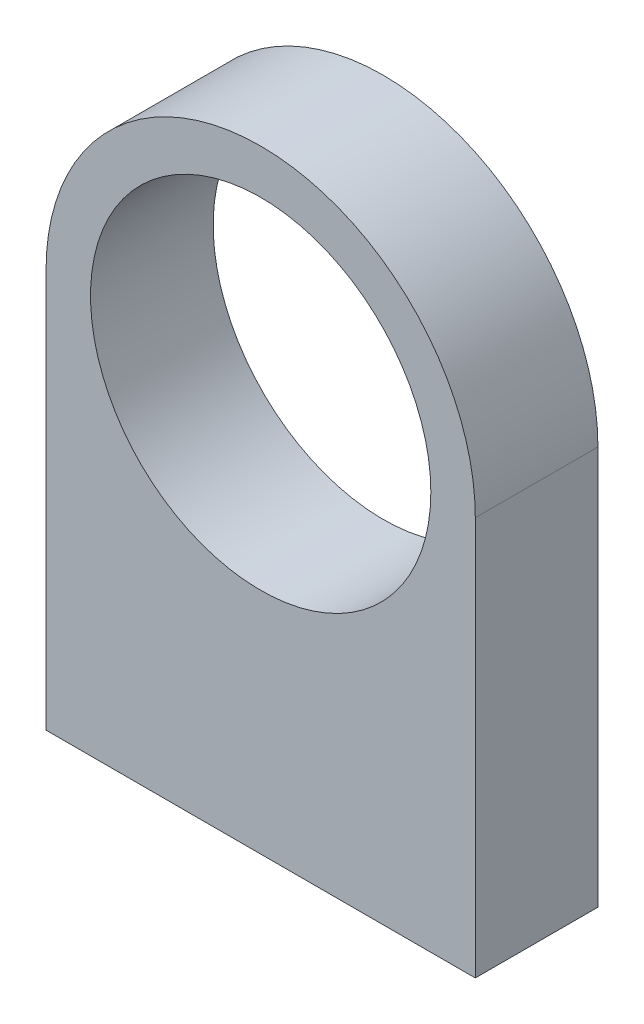
SolidWorks part; units mm, degrees
ref_plane "Plan de face" through (0, 0, 0) normal (0, 0, 1) x (1, 0, 0)
ref_plane "Plan de dessus" through (0, 0, 0) normal (0, 1, 0) x (1, 0, 0)
ref_plane "Plan de droite" through (0, 0, 0) normal (1, 0, 0) x (0, 0, -1)
sketch "Esquisse1" plane through (0, 0, 0) normal (0, 0, 1) x (1, 0, 0)
  line L1 (-14, 0) -> (14, 0) construction
  line L2 (-14, 0) -> (-14, -26)
  line L3 (-14, -26) -> (14, -26)
  line L4 (14, 0) -> (14, -26)
  circle A0 centre (0, 0) radius 14 construction
  arc A1 (-14, 0) -> (14, 0) centre (0, 0) cw
  circle A2 centre (0, 0) radius 11.1
  dimension "D1" = 28
  dimension "D3" = 22.2
  dimension "D2" = 26
extrude "Boss.-Extru.1" add sketch "Esquisse1" along normal blind 8
sketch "Esquisse2" plane through (0, -26, 0) normal (0, -1, 0) x (1, 0, 0)
  line L0 (-10, 4) -> (10, 4) construction
  line L1 (0, 0) -> (0, 8) construction
  line L2 (-14, 8) -> (14, 8) construction
  line L3 (-14, 8) -> (-14, 0) construction
  circle A0 centre (-10, 4) radius 1.5
  circle A1 centre (10, 4) radius 1.5
  point P8 (0, 4)
  point P9 (0, 4)
  dimension "D1" = 3
  dimension "D2" = 4
extrude "Enlèv. mat.-Extru.1" cut sketch "Esquisse2" against normal blind 15
